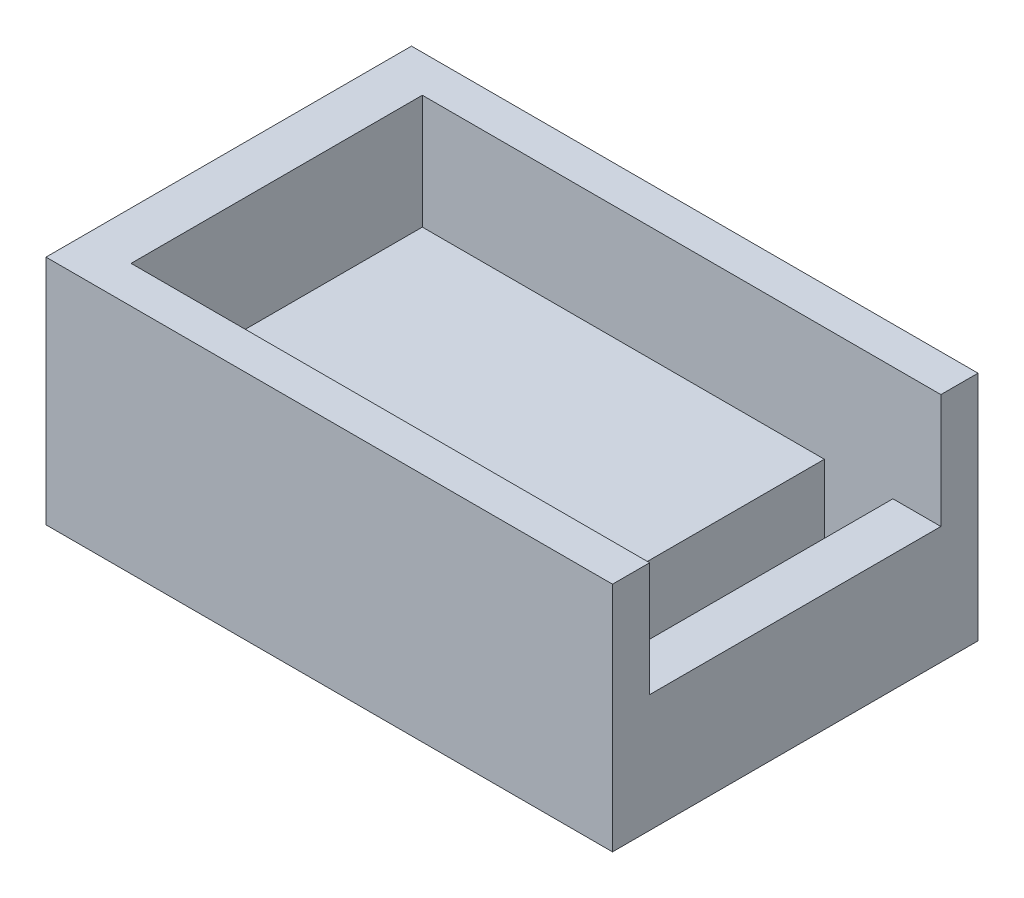
SolidWorks part; units mm, degrees
ref_plane "Front Plane" through (0, 0, 0) normal (0, 0, 1) x (1, 0, 0)
ref_plane "Top Plane" through (0, 0, 0) normal (0, 1, 0) x (1, 0, 0)
ref_plane "Right Plane" through (0, 0, 0) normal (1, 0, 0) x (0, 0, -1)
sketch "Sketch2" plane through (0, 0, 0) normal (0, 1, 0) x (1, 0, 0)
  line L1 (0, 0) -> (24.8, 0)
  line L2 (0, 0) -> (0, -16)
  line L3 (0, -16) -> (24.8, -16)
  line L4 (24.8, 0) -> (24.8, -16)
  line L5 (19.7, -1.625) -> (22.7, -1.625)
  line L6 (19.7, -1.625) -> (19.7, -14.375)
  line L7 (19.7, -14.375) -> (22.7, -14.375)
  line L8 (22.7, -1.625) -> (22.7, -14.375)
  point P9 (22.7, -8)
  point P10 (24.8, -8)
  dimension "D1" = 12.75
  dimension "D2" = 3
  dimension "D3" = 24.8
  dimension "D4" = 2.1
  dimension "D5" = 16
extrude "Boss-Extrude1" add sketch "Sketch2" along normal blind 5.15
sketch "Sketch4" plane through (0, 5.15, 0) normal (0, 1, 0) x (1, 0, 0)
  line L0 (19.7, -1.625) -> (19.7, -14.375)
  line L1 (19.7, -1.625) -> (2.1, -1.625)
  line L2 (19.7, -14.375) -> (2.1, -14.375)
  line L3 (2.1, -1.625) -> (2.1, -14.375)
  line L4 (0, 0) -> (0, -16)
  line L5 (0, -16) -> (24.8, -16)
  line L6 (24.8, -16) -> (24.8, 0)
  line L7 (24.8, 0) -> (0, 0)
  line L8 (0, 0) -> (0, -16)
  line L9 (0, -16) -> (24.8, -16)
  line L10 (24.8, -16) -> (24.8, 0)
  line L11 (24.8, 0) -> (0, 0)
  line L13 (19.7, -14.375) -> (24.8, -14.375)
  line L14 (19.7, -1.625) -> (24.8, -1.625)
  line M9 (0, 0) -> (0, -16)
  line M10 (0, -16) -> (24.8, -16)
  line M11 (24.8, -16) -> (24.8, 0)
  line M12 (24.8, 0) -> (0, 0)
  line M13 (22.7, -14.375) -> (19.7, -14.375)
  line M15 (19.7, -1.625) -> (22.7, -1.625)
  dimension "D2" = 2.1
  dimension "D1" = 0
extrude "Boss-Extrude2" add sketch "Sketch4" along normal blind 5 contours L14 L13 L2 L3 L1 M15 M11 M12 M9 M10 M13
